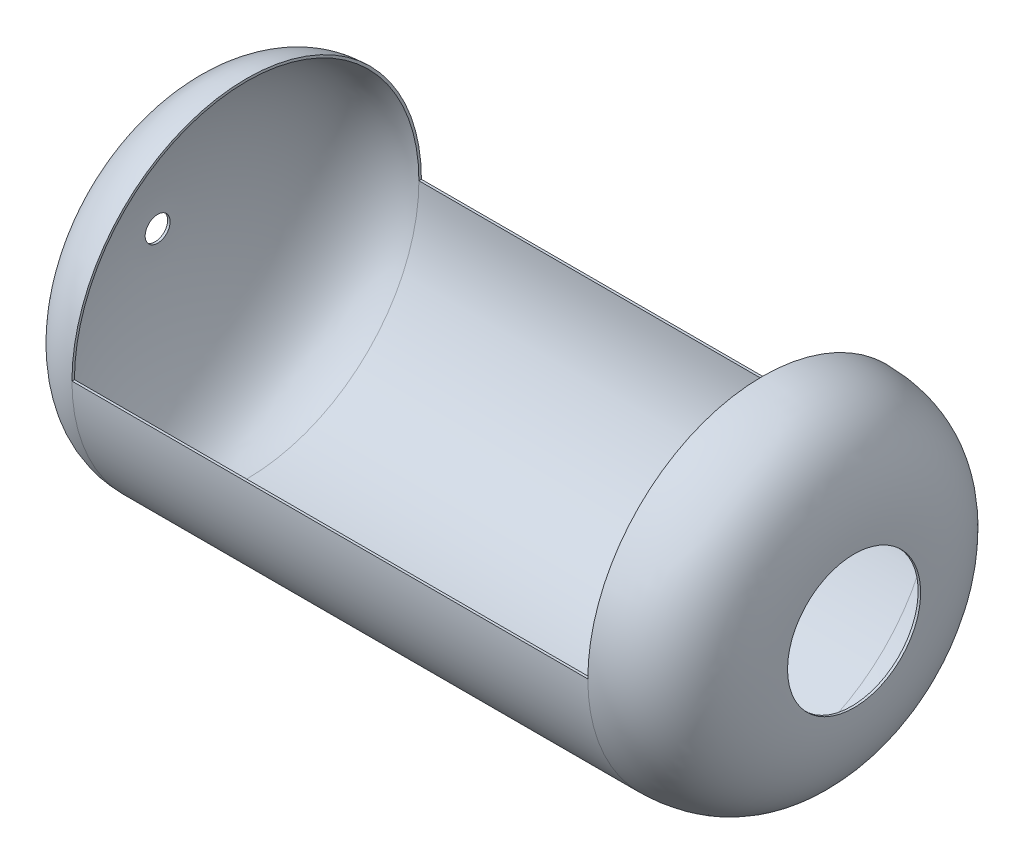
SolidWorks part; units mm, degrees
ref_plane "Front Plane" through (0, 0, 0) normal (0, 0, 1) x (1, 0, 0)
ref_plane "Top Plane" through (0, 0, 0) normal (0, 1, 0) x (1, 0, 0)
ref_plane "Right Plane" through (0, 0, 0) normal (1, 0, 0) x (0, 0, -1)
sketch "Sketch1" plane through (0, 0, 0) normal (0, 1, 0) x (1, 0, 0)
  line L0 (-38.4161, -102.436) -> (581.5839, -102.436)
  line L1 (-396.5921, -312.436) -> (1258.7695, -312.436) construction
  line L2 (-38.4161, -105.436) -> (581.5722, -105.436)
  line L3 (-148.4161, -297.436) -> (-145.4162, -297.4487)
  line L4 (688.5839, -232.436) -> (691.5839, -232.436)
  spline S0 degree 3 poles (-38.4161, -102.436) (-139.4449, -102.6441) (-148.3699, -286.573) (-148.4161, -297.436) knots 0 0 0 0 1 1 1 1
  spline S2 degree 3 poles (581.5839, -102.436) (693.4555, -103.3001) (691.5839, -210.8024) (691.5839, -232.436) knots 0 0 0 0 1 1 1 1
  spline S4 degree 3 poles (-145.4162, -297.4487) (-145.4158, -297.3631) (-145.4143, -297.2091) (-145.4065, -296.7636) (-145.3876, -296.059) (-145.3481, -294.9637) (-145.2705, -293.1962) (-145.1222, -290.4302) (-144.8469, -286.2922) (-144.4591, -281.402) (-143.772, -273.9673) (-142.5563, -263.1242) (-140.4063, -248.1593) (-137.4452, -231.7679) (-133.5543, -214.4771) (-128.6167, -196.8153) (-122.5183, -179.3119) (-115.1499, -162.4979) (-106.41, -146.9032) (-96.2071, -133.0523) (-86.418, -123.386) (-77.7696, -117.0141) (-70.8592, -112.9705) (-63.5047, -109.7164) (-56.9853, -107.7086) (-51.5204, -106.5542) (-47.2941, -105.9222) (-43.6595, -105.5972) (-40.6895, -105.4625) (-39.1712, -105.4376) (-38.4161, -105.436) knots 0.000021 0.000021 0.000021 0.000021 0.007833 0.015646 0.03127 0.046895 0.06252 0.093769 0.125019 0.156268 0.187517 0.250016 0.312515 0.375013 0.437512 0.500011 0.562509 0.625008 0.687507 0.750005 0.812504 0.843753 0.875003 0.906252 0.937501 0.953126 0.968751 0.984375 0.992188 1 1 1 1
  spline S5 degree 3 poles (581.5722, -105.436) (582.4242, -105.4426) (584.1379, -105.4689) (587.4841, -105.5715) (591.5711, -105.7929) (596.3076, -106.2026) (602.4091, -106.9348) (609.6394, -108.1867) (617.7059, -110.1905) (625.1867, -112.6593) (634.4142, -116.5233) (644.6121, -122.339) (654.9138, -130.6304) (663.4693, -139.982) (670.4504, -150.1415) (676.0167, -160.8476) (680.3233, -171.829) (683.5257, -182.807) (685.7821, -193.4984) (687.2534, -203.6189) (687.9614, -211.3398) (688.2994, -216.9475) (688.4596, -220.834) (688.5471, -224.3659) (688.5828, -227.5129) (688.5867, -229.7771) (688.5848, -231.3838) (688.5839, -232.076) (688.5839, -232.436) knots 0.000035 0.000035 0.000035 0.000035 0.007847 0.015659 0.031284 0.046908 0.062533 0.093782 0.125031 0.15628 0.187528 0.250026 0.312524 0.375022 0.43752 0.500017 0.562515 0.625013 0.687511 0.750009 0.812507 0.843755 0.875004 0.906253 0.937502 0.968751 0.984376 1 1 1 1
  dimension "D1" = 110
  dimension "D2" = 110
  dimension "D3" = 620
  dimension "D4" = 195
  dimension "D5" = 130
  dimension "D6" = 15
revolve "Revolve1" add sketch "Sketch1" angle 360 about L1
ref_plane "Plane1" through (-38.4161, 0, 0) normal (1, 0, 0) x (0, 0, -1)
ref_plane "Plane2" through (581.5839, 0, 0) normal (1, 0, 0) x (0, 0, -1)
sketch "Sketch4" plane through (-38.4161, 0, 0) normal (1, 0, 0) x (0, 0, -1)
  line L1 (-737.4959, 357.9485) -> (221.112, 357.9485)
  line L2 (-737.4959, 357.9485) -> (-737.4959, 0)
  line L3 (-737.4959, 0) -> (221.112, 0)
  line L4 (221.112, 357.9485) -> (221.112, 0)
extrude "Cut-Extrude2" cut sketch "Sketch4" along normal up to surface (620 mm away)
